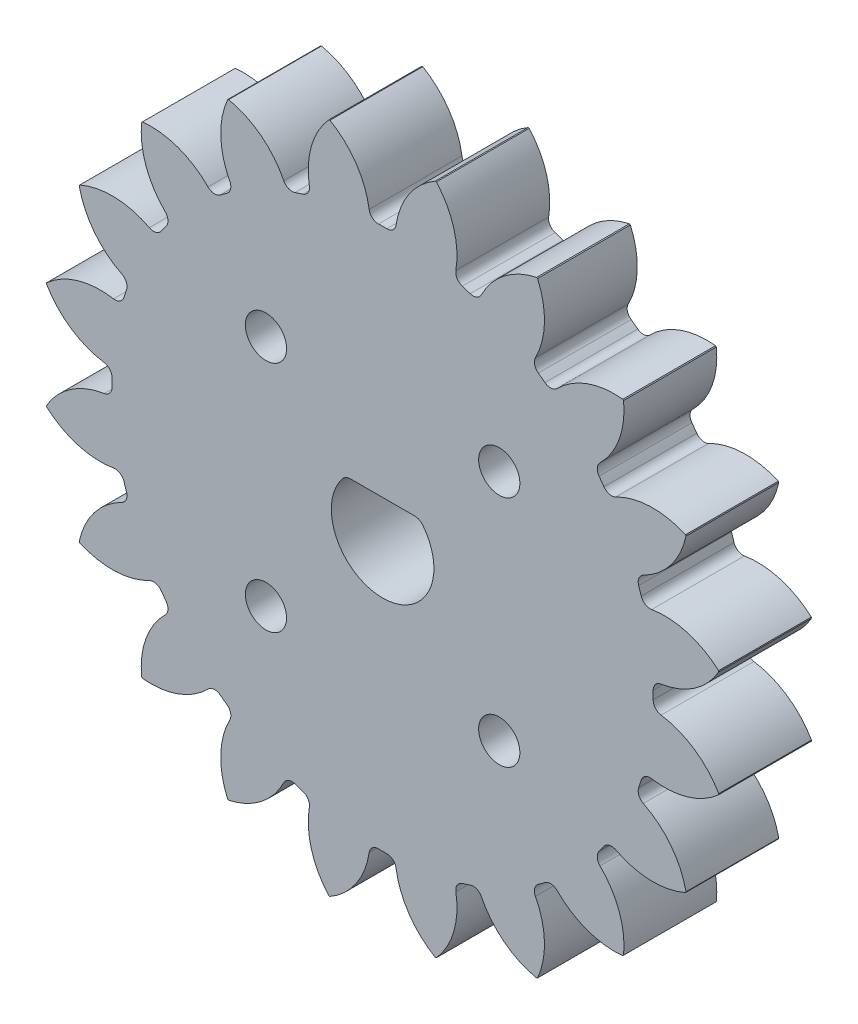
SolidWorks part; units mm, degrees
ref_plane "Front Plane" through (0, 0, 0) normal (0, 0, 1) x (1, 0, 0)
ref_plane "Top Plane" through (0, 0, 0) normal (0, 1, 0) x (1, 0, 0)
ref_plane "Right Plane" through (0, 0, 0) normal (1, 0, 0) x (0, 0, -1)
sketch "Sketch1" plane through (0, 0, 0) normal (0, 0, 1) x (1, 0, 0)
  circle A0 centre (0, 0) radius 30
  circle A1 centre (0, 0) radius 33
  dimension "D1" = 60
  dimension "D2" = 66
extrude "Boss-Extrude1" add sketch "Sketch1" along normal blind 9 contours A1 A0
sketch "Sketch2" plane through (0, 0, 9) normal (0, 0, 1) x (1, 0, 0)
  line L0 (0, 33) -> (0, 0) construction
  line L1 (0, 0) -> (10.1976, 31.3849) construction
  line L2 (0, 0) -> (5.1623, 32.5937) construction
  line L3 (-1.2265, 26.2213) -> (0, 0) construction
  line L4 (-2.3538, 29.9075) -> (2.3538, 29.9075) construction
  line L5 (2.3538, 29.9075) -> (7.0034, 29.1711) construction
  line L6 (-3.2591, 32.8387) -> (0, 23.8843) construction
  circle A0 centre (0, 0) radius 27 construction
  circle A2 centre (0, 0) radius 33 construction
  arc A3 (-5.1104, 32.6019) -> (-1.2265, 26.2213) centre (-9.0076, 25.8574) cw
  circle A4 centre (0, 0) radius 33 construction
  arc A5 (5.1104, 32.6019) -> (1.2265, 26.2213) centre (9.0076, 25.8574) ccw
  circle A6 centre (0, 0) radius 30 construction
  arc A7 (1.2265, 26.2213) -> (-1.2265, 26.2213) centre (0, 0) ccw
  circle M1 centre (0, 0) radius 33
  dimension "D1" = 18
  dimension "D2" = 6
  dimension "D4" = 20
  dimension "D3" = 0.75
extrude "Cut-Extrude1" cut sketch "Sketch2" against normal through all both and the other way through all contours A7 A5 A3 M1
fillet "Fillet1" radius 0.9 2 edges at (1.2265, 26.2213, 4.5) (-1.2265, 26.2213, 4.5)
pattern_circular "CirPattern3" count 20 over 360 about axis through (0, 0, 0) along (0, 0, 1) of "Fillet1", "Cut-Extrude1"
sketch "Sketch3" plane through (0, 0, 9) normal (0, 0, 1) x (1, 0, 0)
  line L1 (-3.5602, 3.475) -> (3.5602, 3.475)
  circle A1 centre (0, 0) radius 4.975
  point P2 (0, 4.975)
  dimension "D1" = 9.95
  dimension "D2" = 1.5
extrude "Cut-Extrude3" cut sketch "Sketch3" against normal through all contours L1 A1
fillet "Fillet2" radius 1 1 edges at (-3.5602, 3.475, 4.5)
fillet "Fillet3" radius 1 1 edges at (3.5602, 3.475, 4.5)
sketch "Sketch4" plane through (0, 0, 9) normal (0, 0, 1) x (1, 0, 0)
  line L0 (0, 0) -> (26.25, 0) construction
  line L1 (0, 0) -> (0, 26.25) construction
  line L2 (18.5616, 18.5616) -> (0, 0) construction
  circle A0 centre (0, 0) radius 26.25
  circle A1 centre (11.3137, 11.3137) radius 2
  circle A2 centre (-11.3137, 11.3137) radius 2
  circle A3 centre (-11.3137, -11.3137) radius 2
  circle A4 centre (11.3137, -11.3137) radius 2
  point P4 (18.5616, 18.5616)
  dimension "D3" = 4
  dimension "D1" = 45
  dimension "D2" = 16
extrude "Cut-Extrude4" cut sketch "Sketch4" against normal through all contours A2 | A1 | A4 | A3
equation "\"Module\"= 3mm"
equation "\"No. Teeth\"= 20"
equation "\"Contact Angle\"= 20"
equation "\"D1@Sketch1\"=\"Module\" * \"No. Teeth\""
equation "\"D2@Sketch1\"=(\"No. Teeth\" + 2) * \"Module\""
equation "\"D1@Sketch2\"=360/\"No. Teeth\""
equation "\"D2@Sketch2\"=2*\"Module\""
equation "\"D4@Sketch2\"=\"Contact Angle\""
equation "\"D1@Fillet1\"=0.3 * \"Module\""
equation "\"D1@CirPattern3\"=\"No. Teeth\""
